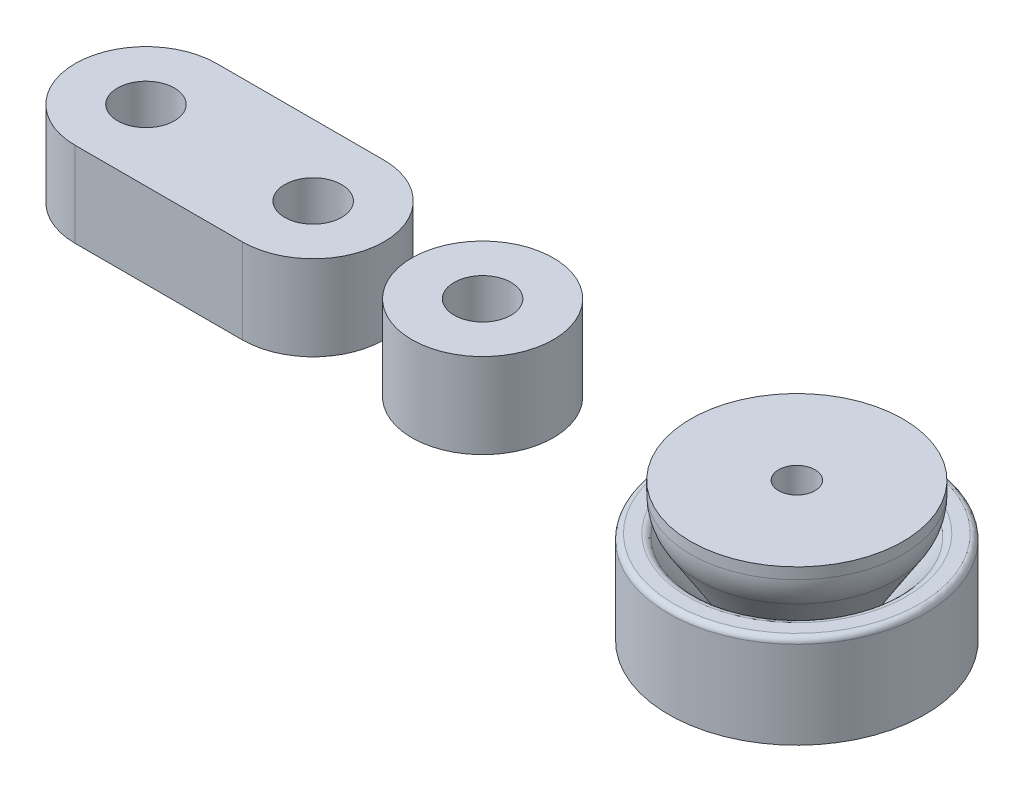
SolidWorks part; units mm, degrees
ref_plane "Front Plane" through (0, 0, 0) normal (0, 0, 1) x (1, 0, 0)
ref_plane "Top Plane" through (0, 0, 0) normal (0, 1, 0) x (1, 0, 0)
ref_plane "Right Plane" through (0, 0, 0) normal (1, 0, 0) x (0, 0, -1)
sketch "Sketch1" plane through (0, 0, 0) normal (0, 0, 1) x (1, 0, 0)
  line L0 (-30.0751, 4.8387) -> (-28.182, 6.7318) construction
  line L1 (-40.882, 0) -> (-15.482, 0) construction
  line L2 (-40.882, 0) -> (-40.882, 4.8387) construction
  line L3 (-40.882, 4.8387) -> (-15.482, 4.8387) construction
  line L4 (-15.482, 0) -> (-15.482, 4.8387) construction
  line L5 (-28.182, 6.7318) -> (-26.2888, 4.8387) construction
  line L6 (-28.182, 6.7318) -> (-28.182, 25.1587) construction
  line L7 (-46.8267, 12.4587) -> (11.2331, 12.4587) construction
  line L8 (-3.2385, 3.8387) -> (-3.2385, 7.3787)
  line L9 (-3.2385, 7.3787) -> (-1.6319, 9.2268)
  line L11 (-1.632, 12.4587) -> (-9.525, 12.4587)
  line L13 (-5.2385, 3.8387) -> (-3.2385, 3.8387)
  line L14 (-1.632, 12.4587) -> (-1.6319, 9.2268)
  line L15 (0, 0) -> (0, 14.9298) construction
  line L18 (0, 2.8387) -> (-4.2419, 2.8387)
  line L19 (0, 0) -> (-11.5, 0)
  line L20 (-11.5, 0) -> (-11.5, 7.8387)
  line L21 (-5.3102, 3.3387) -> (-9.2571, 8.0692)
  line L22 (-9.525, 11.4587) -> (-9.525, 12.4587)
  line L23 (0, 2.8387) -> (0, 0)
  line L24 (-5.6609, 4.0712) -> (-8.8378, 9.0887)
  line L25 (-9.833, 8.3387) -> (-11, 8.3387)
  arc A3 (-9.525, 11.4587) -> (-8.8378, 9.0887) centre (-5.0946, 11.4587) ccw
  arc A5 (-5.2385, 3.8387) -> (-5.6609, 4.0712) centre (-5.2385, 4.3387) cw
  arc A6 (-4.2419, 2.8387) -> (-5.3102, 3.3387) centre (-4.2419, 4.2301) cw
  arc A7 (-9.2571, 8.0692) -> (-9.833, 8.3387) centre (-9.833, 7.5887) ccw
  arc A8 (-11.5, 7.8387) -> (-11, 8.3387) centre (-11, 7.8387) cw
  point P10 (-28.182, 4.8387)
  point P17 (0, 0)
  point P18 (-6.064, 2.8387)
  point P24 (-6.9886, 3.4578)
  point P25 (0, 0)
  point P27 (0, 0)
  point P29 (-5.6393, 2.8387)
  point P30 (-6.064, 2.8387)
  point P31 (0, 0)
  point P33 (-9.1483, 8.3387)
  point P40 (-5.5137, 3.8387)
  point P41 (0, 0)
  point P47 (-4.064, 7.3787)
  point P48 (-2.25, 8.7731)
  point P49 (0, 0)
  point P50 (0, 0)
  point P51 (0, 0)
  dimension "D8" = 7.5
  dimension "D13" = 23
  dimension "D15" = 3.2385
  dimension "D16" = 1
  dimension "D11" = 0.5
  dimension "D18" = 0.2
  dimension "D19" = 0.5
  dimension "D20" = 0.75
  dimension "D21" = 0.5
  dimension "D1" = 4.8387
  dimension "D2" = 20.32
  dimension "D3" = 25.4
  dimension "D4" = 12.7
  dimension "D5" = 1.632
  dimension "D6" = 4.5
  dimension "D7" = 19.05
  dimension "D9" = 2
  dimension "D10" = 5.08
  dimension "D12" = 1
  dimension "D14" = 0.75
  dimension "D17" = 1
  dimension "D22" = 41
revolve "Revolve1" add sketch "Sketch1" angle 360 about L15
split "Split1" [suppressed] bodies to split 106
move or copy body "Body-Move/Copy1" [suppressed] bodies to move or copy 112 copy no translate (1.5, 0, 0)
sketch "Sketch2" [suppressed] plane through (0, 0, 0) normal (1, 0, 0) x (0, 0, -1)
  line L8 (-11.5, 7.8387) -> (-11.5, 0)
  line L9 (-10.2237, 8.3387) -> (-11, 8.3387)
  line L10 (-5.7009, 3.3387) -> (-9.6479, 8.0692)
  line L11 (4.6326, 2.8387) -> (-4.6326, 2.8387)
  line L12 (9.6479, 8.0692) -> (5.7009, 3.3387)
  line L13 (11, 8.3387) -> (10.2237, 8.3387)
  line L14 (11.5, 0) -> (11.5, 7.8387)
  line L15 (-11.5, 0) -> (11.5, 0)
  line L16 (-11.5, 7.8387) -> (-11.5, 0)
  line L17 (-10.2237, 8.3387) -> (-11, 8.3387)
  line L18 (-5.7009, 3.3387) -> (-9.6479, 8.0692)
  line L19 (4.6326, 2.8387) -> (-4.6326, 2.8387)
  line L20 (9.6479, 8.0692) -> (5.7009, 3.3387)
  line L21 (11, 8.3387) -> (10.2237, 8.3387)
  line L22 (11.5, 0) -> (11.5, 7.8387)
  line L23 (-11.5, 0) -> (11.5, 0)
  arc A6 (-11, 8.3387) -> (-11.5, 7.8387) centre (-11, 7.8387) ccw
  arc A7 (-9.6479, 8.0692) -> (-10.2237, 8.3387) centre (-10.2237, 7.5887) ccw
  arc A8 (-5.7009, 3.3387) -> (-4.6326, 2.8387) centre (-4.6326, 4.2301) ccw
  arc A9 (4.6326, 2.8387) -> (5.7009, 3.3387) centre (4.6326, 4.2301) ccw
  arc A10 (10.2237, 8.3387) -> (9.6479, 8.0692) centre (10.2237, 7.5887) ccw
  arc A11 (11.5, 7.8387) -> (11, 8.3387) centre (11, 7.8387) ccw
  arc A12 (-11, 8.3387) -> (-11.5, 7.8387) centre (-11, 7.8387) ccw
  arc A13 (-9.6479, 8.0692) -> (-10.2237, 8.3387) centre (-10.2237, 7.5887) ccw
  arc A14 (-5.7009, 3.3387) -> (-4.6326, 2.8387) centre (-4.6326, 4.2301) ccw
  arc A15 (4.6326, 2.8387) -> (5.7009, 3.3387) centre (4.6326, 4.2301) ccw
  arc A16 (10.2237, 8.3387) -> (9.6479, 8.0692) centre (10.2237, 7.5887) ccw
  arc A17 (11.5, 7.8387) -> (11, 8.3387) centre (11, 7.8387) ccw
  dimension "D1" = 0
extrude "Boss-Extrude1" [suppressed] add sketch "Sketch2" along normal up to next
mirror "Mirror1" [suppressed] about plane through (0, 0, 0) normal (1, 0, 0)
hole_wizard "CSK for #4 Flat Head Socket Cap Screw1" positions "Sketch3" profile "Sketch4" countersink size "#4" standard "ANSI Inch"
sketch "Sketch3" plane through (0, 2.8387, 0) normal (0, 1, 0) x (1, 0, 0)
  point P0 (0, 0)
sketch "Sketch4" plane through (0, 2.8387, 0) normal (1, 0, 0) x (0, 0, 1)
  line L0 (0, 0) -> (0, 5.0406)
  line L1 (0, 5.0406) -> (1.6319, 4.06)
  line L2 (1.6319, 4.06) -> (1.6319, 1.8481)
  line L3 (1.6319, 1.8481) -> (3.2385, 0)
  line L5 (3.2385, 0) -> (0, 0)
  line L6 (-1.632, 1.8481) -> (-3.2385, 0) construction
  line L10 (0, 5.0406) -> (-1.632, 4.06) construction
  line L11 (0, -6.35) -> (0, 107.95) construction
  dimension "Hole Dia." = 3.2639
  dimension "Hole Depth" = 4.06
  dimension "Near C'Sink Dia." = 6.477
  dimension "Near C'Sink Angle" = 82
  dimension "Drill Angle" = 118
sketch "Sketch5" plane through (0, 0, 0) normal (0, 1, 0) x (1, 0, 0)
  line L0 (-58.3807, 0) -> (-43.3807, 0) construction
  line L1 (-58.3807, 6.35) -> (-43.3807, 6.35)
  line L2 (-58.3807, -6.35) -> (-43.3807, -6.35)
  circle A0 centre (-28.182, 0) radius 6.35
  arc A1 (-58.3807, 6.35) -> (-58.3807, -6.35) centre (-58.3807, 0) ccw
  arc A2 (-43.3807, -6.35) -> (-43.3807, 6.35) centre (-43.3807, 0) ccw
  point P6 (-50.8807, 0)
  dimension "D1" = 12.7
  dimension "D2" = 15
extrude "Boss-Extrude2" add sketch "Sketch5" along normal up to vertex (12.4587 mm away) from vertex at 4.8387 separate body starting at point (-26.2888, 4.8387, 0)
hole_wizard "CSK for #10 Flat Head Socket Cap Screw1" positions "Sketch6" profile "Sketch7" countersink size "#10" standard "ANSI Inch" end condition through all
sketch "Sketch6" plane through (0, 4.8387, 0) normal (0, -1, 0) x (-1, 0, 0)
  point P0 (28.182, 0)
  point P4 (43.3807, 0)
  point P7 (58.3807, 0)
sketch "Sketch7" plane through (-28.182, 4.8387, 0) normal (1, 0, 0) x (0, 0, -1)
  line L0 (0, 0) -> (0, 7.62)
  line L1 (0, 7.62) -> (2.5527, 7.62)
  line L2 (2.5527, 7.62) -> (2.5527, 2.7612)
  line L3 (2.5527, 2.7612) -> (4.953, 0)
  line L5 (4.953, 0) -> (0, 0)
  line L6 (-2.5527, 2.7612) -> (-4.953, 0) construction
  line L11 (0, -6.35) -> (0, 107.95) construction
  dimension "Thru Hole Dia." = 5.1054
  dimension "Thru Hole Depth" = 7.62
  dimension "Near C'Sink Dia." = 9.906
  dimension "Near C'Sink Angle" = 82
